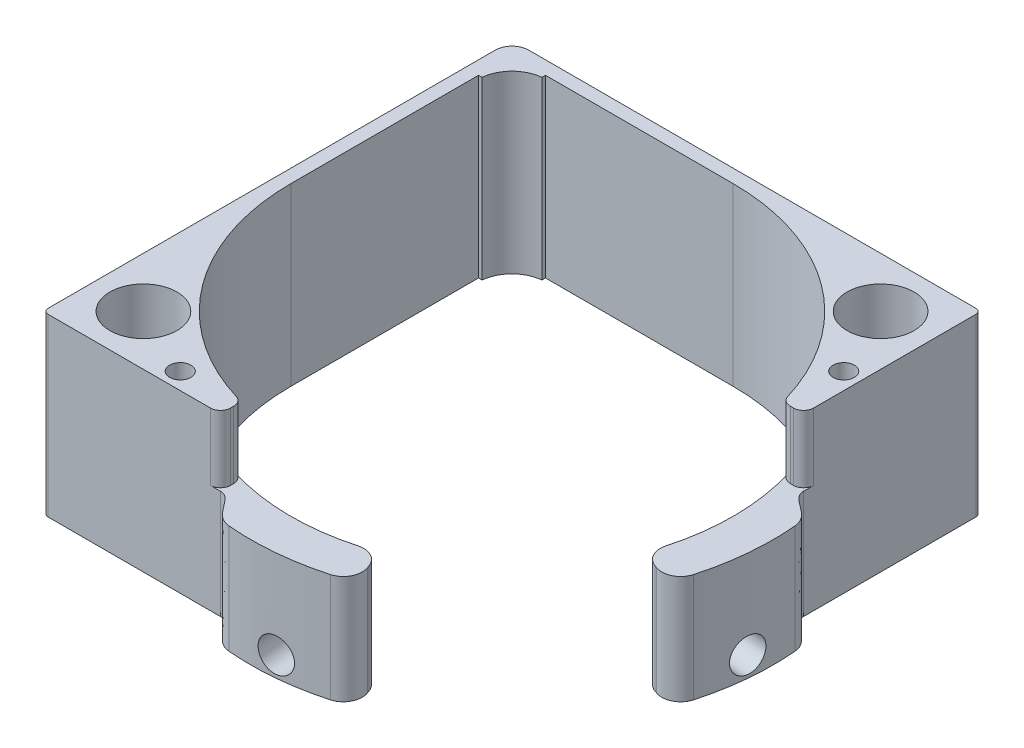
SolidWorks part; units mm, degrees
ref_plane "Front Plane" through (0, 0, 0) normal (0, 0, 1) x (1, 0, 0)
ref_plane "Top Plane" through (0, 0, 0) normal (0, 1, 0) x (1, 0, 0)
ref_plane "Right Plane" through (0, 0, 0) normal (1, 0, 0) x (0, 0, -1)
sketch "Sketch1" plane through (0, 0, 0) normal (0, 1, 0) x (1, 0, 0)
  line L0 (0, 88.9) -> (2.9648, 85.9352) construction
  line L1 (0, 0) -> (33.655, 0)
  line L2 (0, 0) -> (0, 88.9)
  line L3 (0, 88.9) -> (88.9, 88.9)
  line L4 (88.9, 55.245) -> (88.9, 88.9)
  line L5 (84.9459, 55.245) -> (88.9, 55.245)
  line L6 (33.655, 3.9541) -> (33.655, 0)
  line L7 (14.8152, 74.0848) -> (74.0848, 14.8152) construction
  line L8 (74.0848, 14.8152) -> (88.9, 0) construction
  line L9 (33.655, 0) -> (88.9, 0) construction
  line L10 (88.9, 0) -> (88.9, 55.245) construction
  line L11 (2.9648, 85.9352) -> (14.8152, 74.0848) construction
  line L12 (44.45, 86.36) -> (8.89, 86.36)
  line L15 (2.54, 80.01) -> (2.54, 44.45)
  line L19 (2.54, 80.01) -> (8.89, 80.01)
  line L20 (8.89, 86.36) -> (8.89, 80.01)
  arc A0 (33.655, 3.9541) -> (84.9459, 55.245) centre (44.45, 44.45) ccw construction
  arc A1 (2.54, 44.45) -> (33.655, 3.9541) centre (44.45, 44.45) ccw
  arc A2 (84.9459, 55.245) -> (44.45, 86.36) centre (44.45, 44.45) ccw
  arc A3 (44.45, 86.36) -> (14.8152, 74.0848) centre (44.45, 44.45) ccw construction
  arc A4 (14.8152, 74.0848) -> (2.54, 44.45) centre (44.45, 44.45) ccw construction
  dimension "D2" = 83.82
  dimension "D5" = 6.35
  dimension "D1" = 88.9
  dimension "D3" = 2.54
  dimension "D4" = 33.655
extrude "Boss-Extrude1" add sketch "Sketch1" along normal blind 33.274
sketch "Sketch3" plane through (0, 33.274, 0) normal (0, 1, 0) x (1, 0, 0)
  line L2 (2.9648, 85.9352) -> (14.8152, 74.0848) construction
  line L3 (0, 88.9) -> (88.9, 88.9) construction
  circle A0 centre (9.525, 79.375) radius 6.35
  circle A1 centre (79.375, 79.375) radius 6.35
  circle A2 centre (79.375, 9.525) radius 6.35 [skipped]
  circle A3 centre (9.525, 9.525) radius 6.35
  point P2 (16.4338, 9.8675)
  point P8 (66.2802, 38.6581)
  dimension "D1" = 12.7
  dimension "D2" = 2
  dimension "D4" = 69.85
  dimension "D5" = 69.85
  dimension "D6" = 9.525
  dimension "D3" = 2
extrude "Cut-Extrude1" cut sketch "Sketch3" against normal through all
sketch "Sketch4" plane through (0, 0, 0) normal (0, -1, 0) x (1, 0, 0)
  line L0 (40.1332, 4.8915) -> (40.4633, 1.118) construction
  line L1 (93.7915, -48.7668) -> (90.018, -48.4367) construction
  line L2 (33.655, 0) -> (33.655, -3.9541)
  line L3 (74.0848, -14.8152) -> (88.9, 0) construction
  line L8 (59.9527, -1.8568) -> (60.1269, -1.378)
  line L9 (87.0432, -28.9473) -> (87.522, -28.7731)
  line L10 (14.8152, -74.0848) -> (74.0848, -14.8152) construction
  line L11 (84.9459, -55.245) -> (88.9, -55.245)
  line L12 (0, 0) -> (33.655, 0) construction
  line L13 (43.0496, 5.1467) -> (37.2508, 4.6393) construction
  line L14 (36.55, 0) -> (30.056, 0) construction
  line L15 (14.8152, -74.0848) -> (74.0848, -14.8152) construction
  arc A0 (84.9459, -55.245) -> (33.655, -3.9541) centre (44.45, -44.45) ccw construction
  arc A1 (84.9459, -55.245) -> (84.833, -33.24) centre (44.45, -44.45) ccw
  arc A2 (93.7915, -48.7668) -> (92.1638, -31.1605) centre (44.45, -44.45) ccw
  arc A3 (92.3088, -57.2077) -> (31.6923, 3.4088) centre (44.45, -44.45) ccw construction
  arc A4 (88.9, -55.245) -> (90.018, -48.4367) centre (44.45, -44.45) ccw construction
  arc A5 (88.6486, -56.232) -> (32.668, -0.2514) centre (44.45, -44.45) ccw construction
  arc A6 (40.4633, 1.118) -> (33.655, 0) centre (44.45, -44.45) ccw construction
  arc A7 (83.8325, -30.1159) -> (58.7841, -5.0675) centre (44.45, -44.45) ccw construction
  arc A8 (55.66, -4.067) -> (33.655, -3.9541) centre (44.45, -44.45) ccw
  arc A9 (84.9459, -55.245) -> (33.655, -3.9541) centre (44.45, -44.45) ccw construction
  arc A10 (90.993, -27.5097) -> (61.3903, 2.093) centre (44.45, -44.45) ccw construction
  arc A11 (57.7395, 3.2638) -> (40.1332, 4.8915) centre (44.45, -44.45) ccw
  arc A12 (87.522, -28.7731) -> (92.1638, -31.1605) centre (88.7382, -32.1146) cw
  arc A13 (87.0432, -28.9473) -> (84.833, -33.24) centre (88.2594, -32.2889) ccw
  arc A14 (59.9527, -1.8568) -> (55.66, -4.067) centre (56.6111, -0.6406) cw
  arc A15 (60.1269, -1.378) -> (57.7395, 3.2638) centre (56.7854, -0.1618) ccw
  spline S0 degree 3 poles (33.655, 0) (36.195, 0) (36.7594, 4.5964) (40.1332, 4.8915) knots 0 0 0 0 1 1 1 1
  spline S1 degree 3 poles (88.9, -55.245) (88.9, -52.705) (93.4964, -52.1406) (93.7915, -48.7668) knots 0 0 0 0 1 1 1 1
  point P17 (79.473, -9.427)
  point P24 (74.0848, -14.8152)
  dimension "D3" = 50
  dimension "D4" = 3.556
  dimension "D5" = 7.62
  dimension "D6" = 10.16
  dimension "D2" = 100
  dimension "D1" = 7.62
extrude "Boss-Extrude2" add sketch "Sketch4" against normal offset from surface (20.574 mm away) 12.7 up to face at (9.525, 33.274, -3.175)
sketch "Sketch5" plane through (0, 33.274, 0) normal (0, 1, 0) x (1, 0, 0)
  line L0 (14.8152, 74.0848) -> (74.0848, 14.8152) construction
  line L1 (14.8152, 74.0848) -> (74.0848, 14.8152) construction
  line L2 (88.9, 66.04) -> (85.725, 66.04) construction
  line L3 (88.9, 55.245) -> (88.9, 88.9) construction
  line L4 (0, 88.9) -> (88.9, 88.9) construction
  circle A0 centre (85.725, 66.04) radius 2.0193
  circle A1 centre (22.86, 3.175) radius 2.0193
  arc A2 (84.9459, 55.245) -> (44.45, 86.36) centre (44.45, 44.45) ccw construction
  arc A3 (84.9459, 55.245) -> (44.45, 86.36) centre (44.45, 44.45) ccw construction
  circle A4 centre (79.375, 79.375) radius 6.35 construction
  dimension "D1" = 4.0386
  dimension "D2" = 22.86
  dimension "D3" = 6.35
extrude "Cut-Extrude2" cut sketch "Sketch5" against normal through all
ref_plane "Plane1" through (49.0096, 20.574, 4.8697) normal (0.0921, 0, 0.9958) x (0.9958, 0, -0.0921)
sketch "Sketch6" plane through (49.0096, 20.574, 4.8697) normal (0.0921, 0, 0.9958) x (0.9958, 0, -0.0921)
  line L0 (8.8407, 0) -> (-8.8407, 0) construction
  line L1 (-8.8407, -20.574) -> (8.8407, -20.574) construction
  circle A0 centre (0, -16.764) radius 3.175
  point P4 (0, 0)
  dimension "D1" = 6.35
  dimension "D2" = 3.81
extrude "Cut-Extrude3" cut sketch "Sketch6" against normal up to next
ref_plane "Plane2" through (44.45, 0, -44.45) normal (-0.7071, 0, 0.7071) x (0.7071, 0, 0.7071)
mirror "Mirror1" about plane through (44.45, 0, -44.45) normal (-0.7071, 0, 0.7071) of "Cut-Extrude3"
fillet "Fillet1" radius 3.175 1 edges at (0, 16.637, -88.9)
fillet "Fillet2" radius 1.9177 4 edges at (33.655, 26.924, -3.9541) (84.9459, 26.924, -55.245)
fillet "Fillet3" radius 1 2 edges at (88.9, 16.637, -88.9) (0, 16.637, 0)
